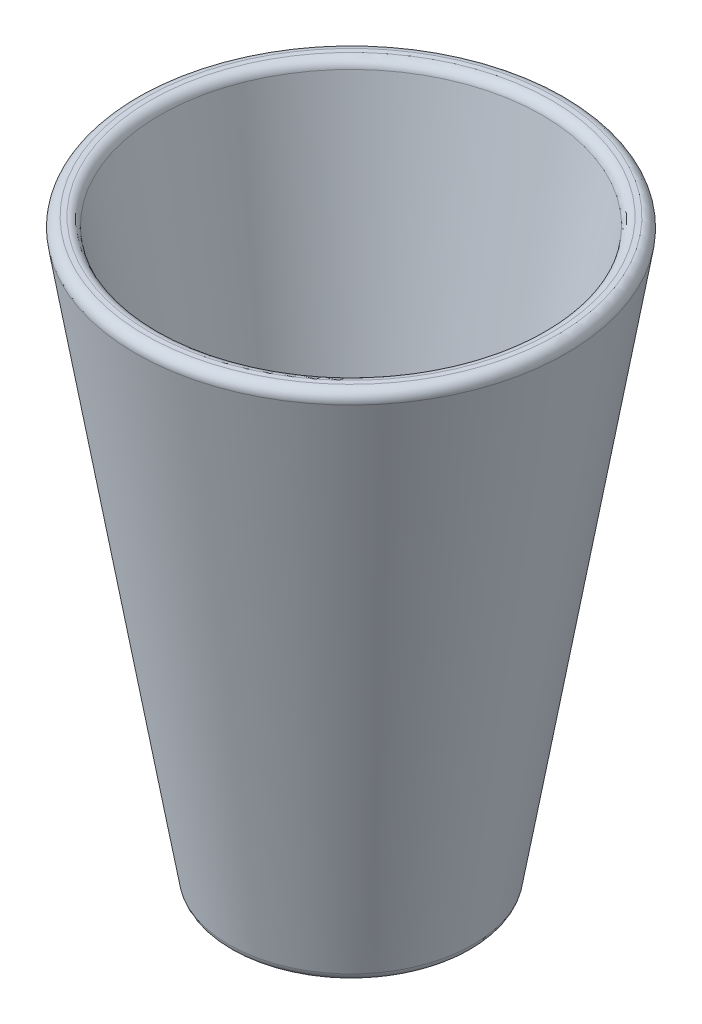
SolidWorks part; units mm, degrees
ref_plane "Front Plane" through (0, 0, 0) normal (0, 0, 1) x (1, 0, 0)
ref_plane "Top Plane" through (0, 0, 0) normal (0, 1, 0) x (1, 0, 0)
ref_plane "Right Plane" through (0, 0, 0) normal (1, 0, 0) x (0, 0, -1)
sketch "Sketch1" plane through (0, 0, 0) normal (0, 0, 1) x (1, 0, 0)
  line L0 (0, -573.8076) -> (0, -623.8076)
  line L1 (400, 576.1924) -> (450.6945, 576.1924)
  line L2 (450.6945, 576.1924) -> (250, -623.8076)
  line L3 (250, -623.8076) -> (0, -623.8076)
  line L4 (0, -573.8076) -> (207.6678, -573.8076)
  line L5 (207.6678, -573.8076) -> (400, 576.1924)
  line L6 (0, 411.8694) -> (0, -426.2426) construction
  dimension "D1" = 1200
  dimension "D2" = 250
  dimension "D3" = 50
  dimension "D4" = 50
  dimension "D5" = 400
revolve "Revolve1" add sketch "Sketch1" angle 360 about L6
fillet "Fillet1" radius 20 3 edges at (0, 576.1924, 450.6945) (0, -623.8076, 250) (0, 576.1924, 400)
